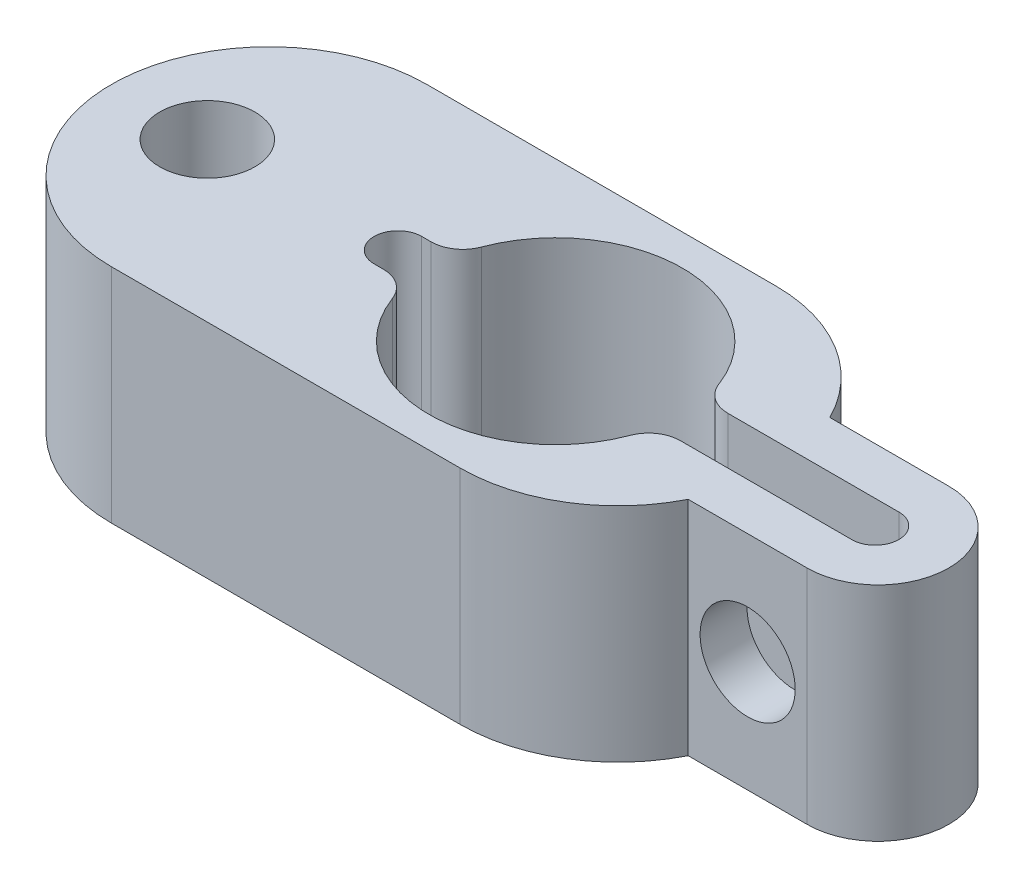
SolidWorks part; units mm, degrees
ref_plane "Front Plane" through (0, 0, 0) normal (0, 0, 1) x (1, 0, 0)
ref_plane "Top Plane" through (0, 0, 0) normal (0, 1, 0) x (1, 0, 0)
ref_plane "Right Plane" through (0, 0, 0) normal (1, 0, 0) x (0, 0, -1)
sketch "Sketch1" plane through (0, 0, 0) normal (0, 1, 0) x (1, 0, 0)
  line L0 (-19.5138, 2.2337) -> (-15.7638, 2.2337)
  line L1 (-18.984, 0) -> (-13.5301, 0) construction
  line L2 (-34.9579, 4.9739) -> (-23.9579, 4.9739)
  line L3 (-19.5138, -2.2337) -> (-15.7638, -2.2337)
  line L6 (-34.9579, -4.9739) -> (-23.9579, -4.9739)
  arc A4 (-19.5138, 2.2337) -> (-23.9579, 4.9739) centre (-23.9579, 0) ccw
  arc A5 (-15.7638, 2.2337) -> (-15.7638, -2.2337) centre (-15.7638, 0) cw
  arc A7 (-34.9579, 4.9739) -> (-34.9579, -4.9739) centre (-34.9579, 0) ccw
  arc A8 (-19.5138, -2.2337) -> (-23.9579, -4.9739) centre (-23.9579, 0) cw
  dimension "D1" = 3.75
extrude "Boss-Extrude2" add sketch "Sketch1" along normal blind 7
sketch "Sketch2" plane through (0, 0, 0) normal (0, 1, 0) x (1, 0, 0)
  line L0 (-15.7638, -2.2337) -> (-15.7638, -0.7546) construction
  line L1 (-21.9181, -0.0059) -> (-16.1096, -0.0059) construction
  line L2 (-15.7638, -0.7546) -> (-21.2377, -0.7546)
  line L3 (-36.9181, -1.4867) -> (-36.9181, 1.5133) construction
  line L4 (-15.8439, 0.7411) -> (-21.2371, 0.7411)
  line L5 (-21.9181, -0.0059) -> (-25.9181, -0.0059) construction
  line L6 (-30.5979, -0.7559) -> (-30.8906, -0.7559)
  line L7 (-30.8906, 0.7441) -> (-30.5979, 0.7441)
  arc A3 (-15.7638, -0.7546) -> (-15.8439, 0.7411) centre (-15.8439, -0.0089) ccw
  circle A4 centre (-36.9181, 0.0133) radius 1.5
  arc A6 (-22.1745, 1.3928) -> (-21.2371, 0.7411) centre (-21.2371, 1.7411) ccw
  arc A7 (-21.2377, -0.7546) -> (-22.1745, -1.4046) centre (-21.2377, -1.7546) ccw
  arc A8 (-30.8906, -0.7559) -> (-30.8906, 0.7441) centre (-30.8906, -0.0059) cw
  arc A9 (-22.1745, -1.4046) -> (-29.6612, -1.4056) centre (-25.9181, -0.0059) cw
  arc A10 (-22.1745, 1.3928) -> (-29.6612, 1.3938) centre (-25.9181, -0.0059) ccw
  arc A11 (-30.5979, -0.7559) -> (-29.6612, -1.4056) centre (-30.5979, -1.7559) cw
  arc A12 (-30.5979, 0.7441) -> (-29.6612, 1.3938) centre (-30.5979, 1.7441) ccw
  point P28 (-34.9509, -0.7559)
  point P31 (-29.8434, -0.7559)
  point P34 (-29.8434, 0.7441)
  dimension "D1" = 3
  dimension "D2" = 1
extrude "Cut-Extrude4" cut sketch "Sketch2" along normal through all
sketch "Sketch4" plane through (0, 0, -2.2337) normal (0, 0, -1) x (-1, 0, 0)
  line L0 (17.6388, 7) -> (17.6388, 0) construction
  line L1 (15.7638, 7) -> (19.5138, 7) construction
  line L2 (15.7638, 0) -> (19.5138, 0) construction
  circle A0 centre (17.6388, 3.5) radius 1.5
  dimension "D1" = 3
extrude "Cut-Extrude5" cut sketch "Sketch4" against normal through all
